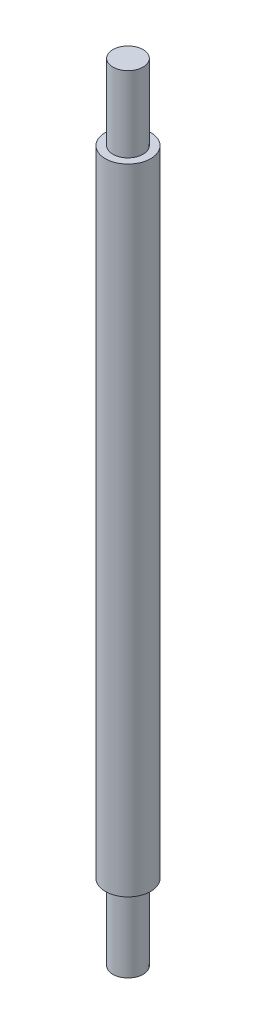
SolidWorks part; units mm, degrees
ref_plane "Front Plane" through (0, 0, 0) normal (0, 0, 1) x (1, 0, 0)
ref_plane "Top Plane" through (0, 0, 0) normal (0, 1, 0) x (1, 0, 0)
ref_plane "Right Plane" through (0, 0, 0) normal (1, 0, 0) x (0, 0, -1)
sketch "Sketch1" plane through (0, 0, 0) normal (0, 0, 1) x (1, 0, 0)
  line L0 (0, 0) -> (2, 0)
  line L1 (2, 0) -> (2, 10)
  line L2 (2, 10) -> (3, 10)
  line L3 (3, 10) -> (3, 94)
  line L4 (3, 94) -> (2, 94)
  line L5 (2, 94) -> (2, 104)
  line L6 (2, 104) -> (0, 104)
  line L7 (0, 104) -> (0, 0)
  point P3 (1, 0)
  dimension "D1" = 2
  dimension "D2" = 2
  dimension "D3" = 3
  dimension "D4" = 104
  dimension "D5" = 10
  dimension "D6" = 10
revolve "Revolve1" add sketch "Sketch1" angle 360 about L7
